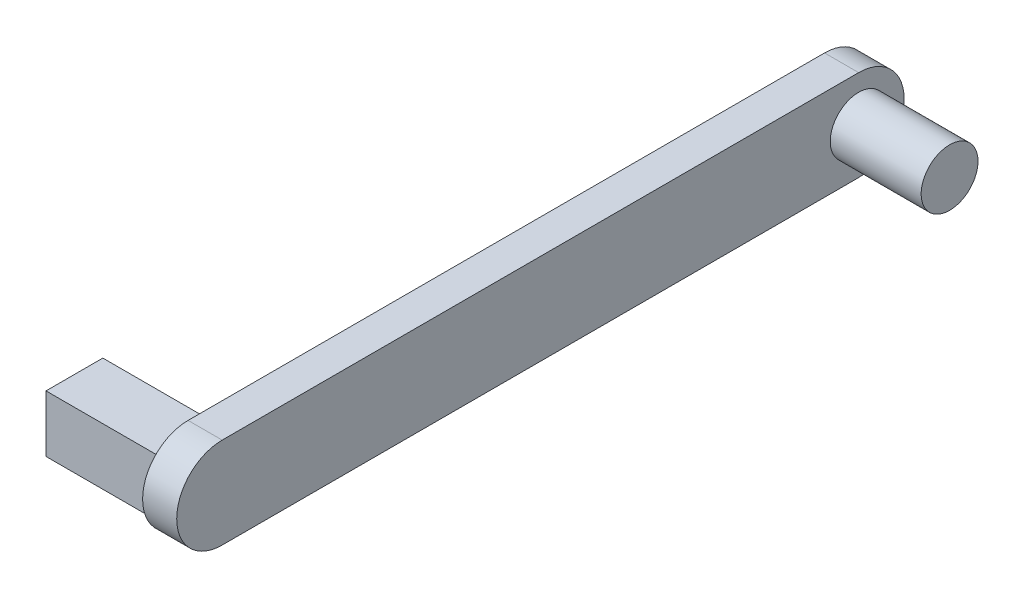
SolidWorks part; units mm, degrees
ref_plane "Front Plane" through (0, 0, 0) normal (0, 0, 1) x (1, 0, 0)
ref_plane "Top Plane" through (0, 0, 0) normal (0, 1, 0) x (1, 0, 0)
ref_plane "Right Plane" through (0, 0, 0) normal (1, 0, 0) x (0, 0, -1)
sketch "Sketch1" plane through (0, 0, 0) normal (1, 0, 0) x (0, 0, -1)
  circle A0 centre (0, 0) radius 3.81
  dimension "D1" = 7.62
extrude "Boss-Extrude1" add sketch "Sketch1" along normal blind 3.048
sketch "Sketch4" plane through (3.048, 0, 0) normal (1, 0, 0) x (0, 0, -1)
  line L0 (0, 0) -> (71.12, 0) construction
  line L1 (0, 5.08) -> (71.12, 5.08)
  line L2 (0, -5.08) -> (71.12, -5.08)
  arc A0 (0, 5.08) -> (0, -5.08) centre (0, 0) ccw
  arc A1 (71.12, -5.08) -> (71.12, 5.08) centre (71.12, 0) ccw
  point P3 (35.56, 0)
  dimension "D2" = 5.08
  dimension "D1" = 71.12
extrude "Boss-Extrude5" add sketch "Sketch4" against normal blind 3.81
sketch "Sketch5" plane through (3.048, 0, 0) normal (1, 0, 0) x (0, 0, -1)
  circle A0 centre (71.12, 0) radius 3.175
  arc A1 (71.12, -5.08) -> (71.12, 5.08) centre (71.12, 0) ccw construction
  dimension "D1" = 6.35
extrude "Boss-Extrude6" add sketch "Sketch5" along normal blind 10.16
sketch "Sketch6" plane through (-0.762, 0, 0) normal (-1, 0, 0) x (0, 0, 1)
  line L1 (3.175, 3.175) -> (-3.175, 3.175)
  line L2 (3.175, 3.175) -> (3.175, -3.175)
  line L3 (3.175, -3.175) -> (-3.175, -3.175)
  line L4 (-3.175, 3.175) -> (-3.175, -3.175)
  line L5 (3.175, 3.175) -> (-3.175, -3.175) construction
  line L6 (3.175, -3.175) -> (-3.175, 3.175) construction
  point P0 (0, 0)
  dimension "D1" = 6.35
extrude "Boss-Extrude7" add sketch "Sketch6" along normal blind 12.7
